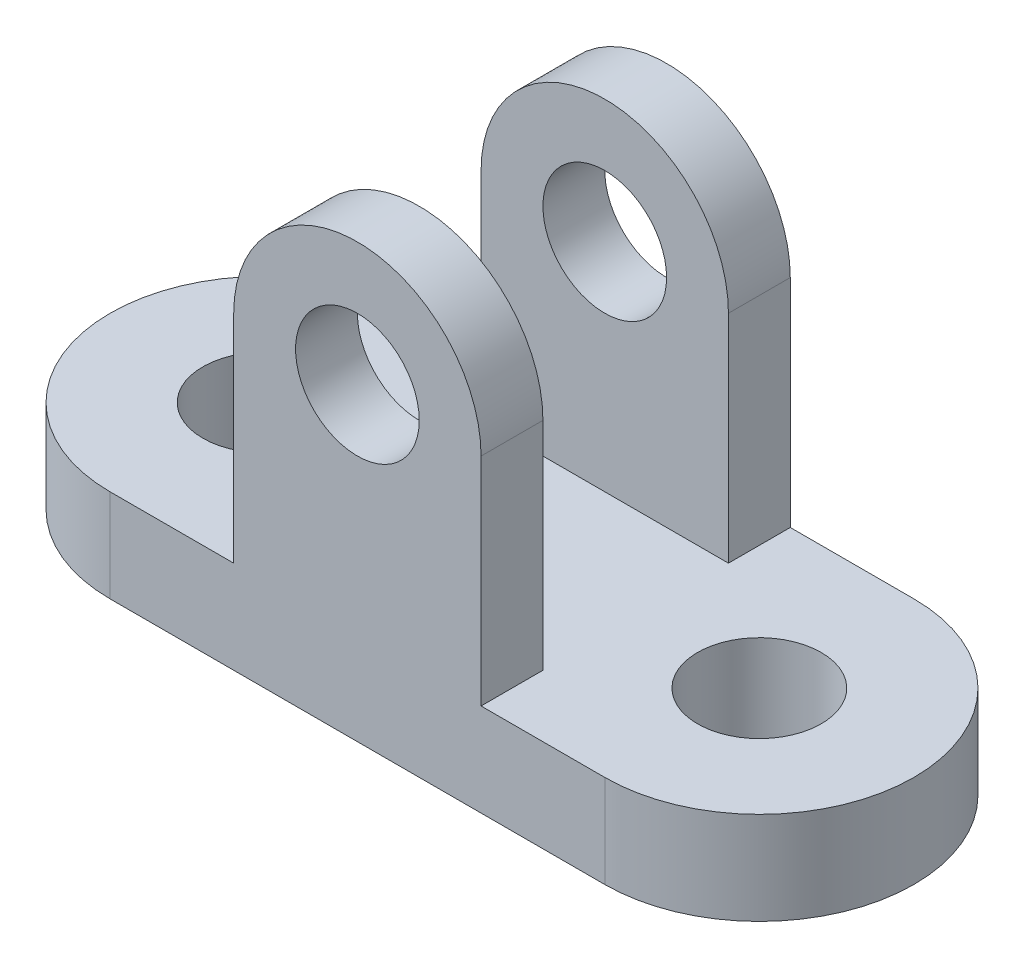
SolidWorks part; units mm, degrees
ref_plane "Front Plane" through (0, 0, 0) normal (0, 0, 1) x (1, 0, 0)
ref_plane "Top Plane" through (0, 0, 0) normal (0, 1, 0) x (1, 0, 0)
ref_plane "Right Plane" through (0, 0, 0) normal (1, 0, 0) x (0, 0, -1)
sketch "Sketch1" plane through (0, 0, 0) normal (0, 1, 0) x (1, 0, 0)
  line L0 (-40, 0) -> (40, 0) construction
  line L1 (-40, 25) -> (40, 25)
  line L2 (-40, -25) -> (40, -25)
  line L3 (0, 0) -> (0, -13.0579) construction
  arc A0 (-40, 25) -> (-40, -25) centre (-40, 0) ccw
  arc A1 (40, -25) -> (40, 25) centre (40, 0) ccw
  circle A2 centre (-40, 0) radius 10
  circle A3 centre (40, 0) radius 10
  point P2 (0, 0)
  dimension "D2" = 25
  dimension "D3" = 20
  dimension "D1" = 80
extrude "Boss-Extrude1" add sketch "Sketch1" along normal blind 15
sketch "Sketch2" plane through (0, 0, 25) normal (0, 0, 1) x (1, 0, 0)
  line L0 (0, 0) -> (0, 50) construction
  line L1 (-40, 0) -> (40, 0) construction
  line L2 (-20, 50) -> (20, 50)
  line L3 (-20, 50) -> (-20, 0)
  line L4 (-20, 0) -> (20, 0)
  line L5 (20, 50) -> (20, 0)
  circle A0 centre (0, 50) radius 20
  circle A1 centre (0, 50) radius 10
  line M2 (-40, 0) -> (40, 0)
  line M4 (40, 15) -> (-40, 15)
  dimension "D1" = 40
  dimension "D2" = 20
  dimension "D3" = 50
extrude "Boss-Extrude2" add sketch "Sketch2" against normal up to surface (50 mm away) contours L0 L5 A0 M4 | L0 A0 L2 A1 | A1 L2 A0 | A0 L0 A1 L2 | L0 A0 L3 M4 | L0 L3 M2 M4 | L0 L4 L5 M4
sketch "Sketch3" plane through (0, 15, 0) normal (0, 1, 0) x (1, 0, 0)
  line L0 (40, 25) -> (20, 25) construction
  line L1 (-29.0397, -15) -> (29.0397, -15)
  line L2 (-29.0397, -15) -> (-29.0397, 15)
  line L3 (-29.0397, 15) -> (29.0397, 15)
  line L4 (29.0397, -15) -> (29.0397, 15)
  line L5 (-29.0397, -15) -> (29.0397, 15) construction
  line L6 (-29.0397, 15) -> (29.0397, -15) construction
  point P0 (0, 0)
  dimension "D1" = 10
extrude "Cut-Extrude1" cut sketch "Sketch3" along normal through all
